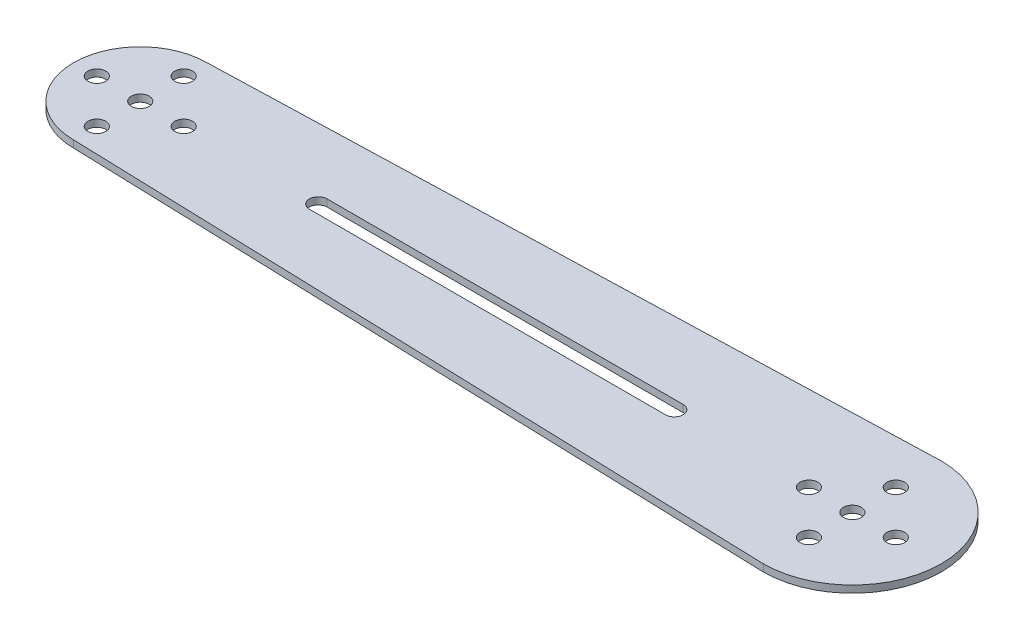
SolidWorks part; units mm, degrees
ref_plane "Front Plane" through (0, 0, 0) normal (0, 0, 1) x (1, 0, 0)
ref_plane "Top Plane" through (0, 0, 0) normal (0, 1, 0) x (1, 0, 0)
ref_plane "Right Plane" through (0, 0, 0) normal (1, 0, 0) x (0, 0, -1)
sketch "Sketch2" plane through (0, 0, 0) normal (0, 1, 0) x (1, 0, 0)
  line L0 (-155.0973, 0) -> (170.648, 0) construction
  line L1 (0, 82.4594) -> (0, -74.2748) construction
  line L2 (100, -40.9921) -> (100, 25) construction
  line L3 (-100, 48.0857) -> (-100, -40.9921) construction
  line L4 (100, 25) -> (-100, 18.75)
  line L5 (100, -25) -> (-100, -18.75)
  arc A2 (100, -25) -> (100, 25) centre (100, 0) ccw
  arc A3 (-100, 18.75) -> (-100, -18.75) centre (-100, 0) ccw
  point P3 (100, 0)
  point P6 (-100, 0)
  point P15 (100, -25)
  point P16 (100, 25)
  point P17 (-100, -18.75)
  point P19 (-100, 18.75)
  dimension "D3" = 50
  dimension "D4" = 37.5
  dimension "D1" = 100
  dimension "D2" = 100
extrude "Boss-Extrude1" add sketch "Sketch2" along normal blind 2
sketch "Sketch4" plane through (0, 2, 0) normal (0, 1, 0) x (1, 0, 0)
  line L0 (-123.9495, 0) -> (119.0142, 0) construction
  line L1 (0, 42.9025) -> (0, -31.7629) construction
  line L2 (100, 42.9025) -> (100, -35.5101) construction
  line L3 (-100, 42.9025) -> (-100, -35.5101) construction
  circle A0 centre (100, 12.2) radius 2.5
  circle A1 centre (100, -12.2) radius 2.5
  circle A2 centre (112.2, 0) radius 2.5
  circle A3 centre (87.8, 0) radius 2.5
  circle A4 centre (-100, 12.2) radius 2.5
  circle A5 centre (-87.8, 0) radius 2.5
  circle A6 centre (-112.2, 0) radius 2.5
  circle A7 centre (-100, -12.2) radius 2.5
  point P9 (100, 12.2)
  point P10 (100, 0)
  point P11 (112.2, 0)
  point P12 (-100, 0)
  point P13 (-100, 12.2)
  point P14 (100, -12.2)
  point P15 (87.8, 0)
  point P20 (100, 0)
  point P24 (-87.8, 0)
  point P25 (-100, -12.2)
  point P26 (-112.2, 0)
  point P31 (-100, 0)
  dimension "D1" = 100
  dimension "D6" = 5
  dimension "D7" = 5
  dimension "D8" = 5
  dimension "D9" = 5
  dimension "D10" = 5
  dimension "D11" = 5
  dimension "D12" = 5
  dimension "D13" = 5
  dimension "D2" = 12.2
  dimension "D4" = 12.2
  dimension "D14" = 100
  dimension "D15" = 100
  dimension "D3" = 4
  dimension "D5" = 4
hole_wizard "Ø5.0mm Dowel Hole1" positions "Sketch9" profile "Sketch10" hole size "Ø5.0" standard "ANSI Metric" end condition up to next
sketch "Sketch9" plane through (0, 2, 0) normal (0, 1, 0) x (1, 0, 0)
  point P0 (100, 0)
  point P3 (-100, 0)
sketch "Sketch10" plane through (100, 2, 0) normal (1, 0, 0) x (0, 0, 1)
  line L0 (0, 0) -> (0, 2)
  line L1 (0, 2) -> (2.5, 2)
  line L2 (2.5, 2) -> (2.5, 0)
  line L5 (2.5, 0) -> (0, 0)
  line L11 (0, -6.35) -> (0, 107.95) construction
  dimension "Thru Hole Dia." = 5
  dimension "Thru Hole Depth" = 2
extrude "Cut-Extrude1" cut sketch "Sketch4" against normal up to next
sketch "Sketch11" plane through (0, 2, 0) normal (0, 1, 0) x (1, 0, 0)
  line L0 (0, 40.9767) -> (0, -46.3977) construction
  line L1 (-109.4412, 0) -> (117.2856, 0) construction
  point P6 (-50, 0)
  point P7 (50, 0)
  dimension "D1" = 50
sketch "Sketch16" plane through (0, 2, 0) normal (0, 1, 0) x (1, 0, 0)
  line L0 (-50, -2.5) -> (50, -2.5)
  line L1 (-50, 2.5) -> (50, 2.5)
  arc A0 (-50, 2.5) -> (-50, -2.5) centre (-50, 0) ccw
  arc A1 (50, -2.5) -> (50, 2.5) centre (50, 0) ccw
extrude "Cut-Extrude2" cut sketch "Sketch16" against normal up to next
equation "\"Length\"= 200"
equation "\"Width\"= 50"
equation "\"D1@Sketch2\"=\"Length\"/2"
equation "\"D2@Sketch2\"=\"Length\"/2"
equation "\"D4@Sketch2\"=\"Width\"*0.75"
equation "\"thick\"=2"
equation "\"D1@Boss-Extrude1\"=\"thick\""
equation "\"D3@Sketch2\"=\"Width\""
equation "\"D1@Sketch4\"=\"Length\"/2"
equation "\"External_HoleDIa\"=5"
equation "\"D13@Sketch4\"=\"External_HoleDIa\""
equation "\"D12@Sketch4\"=\"External_HoleDIa\""
equation "\"D10@Sketch4\"=\"External_HoleDIa\""
equation "\"D11@Sketch4\"=\"External_HoleDIa\""
equation "\"D7@Sketch4\"=\"External_HoleDIa\""
equation "\"D8@Sketch4\"=\"External_HoleDIa\""
equation "\"D9@Sketch4\"=\"External_HoleDIa\""
equation "\"D6@Sketch4\"=\"External_HoleDIa\""
equation "\"D1@Sketch11\"=\"Length\"/4"
equation "\"D14@Sketch4\"=\"Length\"/2"
equation "\"D15@Sketch4\"=\"Length\"/2"
